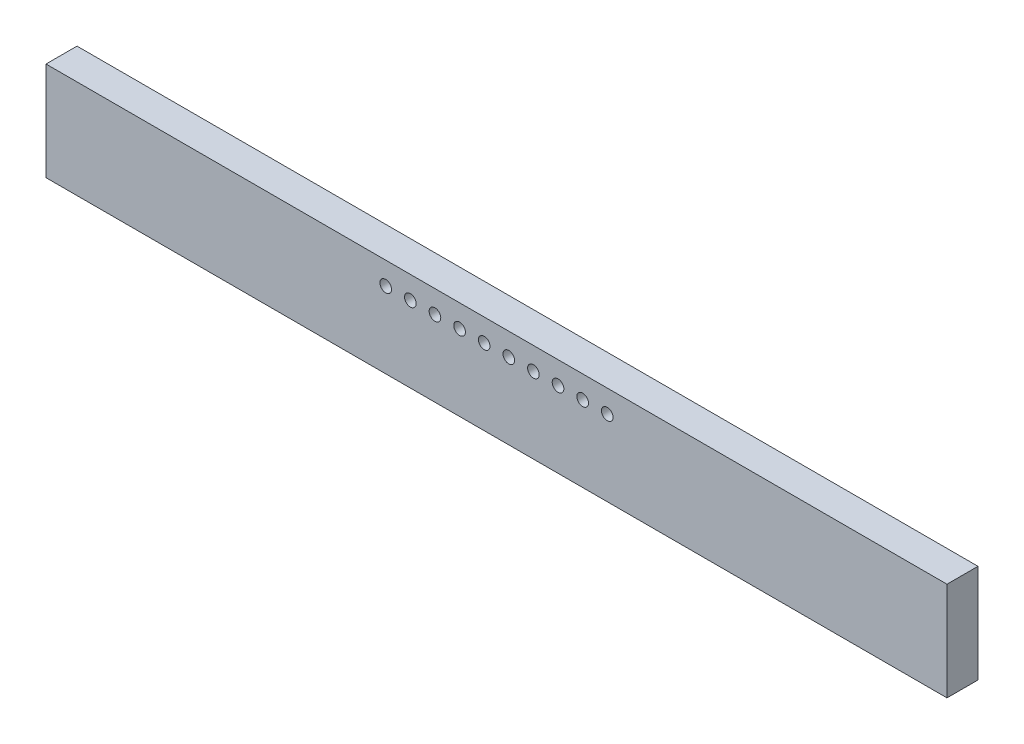
SolidWorks part; units mm, degrees
ref_plane "Front Plane" through (0, 0, 0) normal (0, 0, 1) x (1, 0, 0)
ref_plane "Top Plane" through (0, 0, 0) normal (0, 1, 0) x (1, 0, 0)
ref_plane "Right Plane" through (0, 0, 0) normal (1, 0, 0) x (0, 0, -1)
sketch "Sketch1" plane through (0, 0, 0) normal (0, 0, 1) x (1, 0, 0)
  line L1 (-23.241, -2.54) -> (23.241, -2.54)
  line L2 (-23.241, -2.54) -> (-23.241, 2.54)
  line L3 (-23.241, 2.54) -> (23.241, 2.54)
  line L4 (23.241, -2.54) -> (23.241, 2.54)
  line L5 (-23.241, -2.54) -> (23.241, 2.54) construction
  line L6 (-23.241, 2.54) -> (23.241, -2.54) construction
  point P0 (0, 0)
  dimension "D1" = 46.482
  dimension "D2" = 5.08
extrude "Boss-Extrude1" add sketch "Sketch1" along normal blind 1.6 contours L2 L1 L4 L3
sketch "Sketch2" plane through (0, 0, 1.6) normal (0, 0, 1) x (1, 0, 0)
  line L0 (-5.64, 1.305) -> (-5.79, 1.455) construction
  line L4 (-5.64, 1.455) -> (-5.79, 1.455)
  line L5 (-5.79, 1.455) -> (-5.79, 1.305)
  line L6 (-5.79, 1.305) -> (-5.64, 1.305)
  line L7 (-5.64, 1.305) -> (-5.64, 1.455)
  line L8 (-5.64, 1.455) -> (-5.79, 1.455)
  line L9 (-5.79, 1.455) -> (-5.79, 1.305)
  line L10 (-5.79, 1.305) -> (-5.64, 1.305)
  line L11 (-5.64, 1.305) -> (-5.64, 1.455)
  circle A0 centre (-5.715, 1.38) radius 0.3
  circle A1 centre (-4.445, 1.38) radius 0.3
  circle A2 centre (-3.175, 1.38) radius 0.3
  circle A3 centre (-1.905, 1.38) radius 0.3
  circle A4 centre (-0.635, 1.38) radius 0.3
  circle A5 centre (0.635, 1.38) radius 0.3
  circle A6 centre (1.905, 1.38) radius 0.3
  circle A7 centre (3.175, 1.38) radius 0.3
  circle A8 centre (4.445, 1.38) radius 0.3
  circle A9 centre (5.715, 1.38) radius 0.3
  dimension "D2" = 10
  dimension "D1" = 0
extrude "Cut-Extrude1" cut sketch "Sketch2" against normal through all
sketch "Sketch3" plane through (0, 0, 1.6) normal (0, 0, 1) x (1, 0, 0)
  line L0 (-23.241, 2.54) -> (-20.701, 0) construction
  line L1 (-20.701, 0) -> (-23.241, -2.54) construction
  line L2 (-23.241, -2.54) -> (-23.241, 2.54) construction
  line L5 (0, -0.88) -> (0, 0.88) construction
  line L6 (20.701, 0) -> (23.241, -2.54) construction
  line L7 (23.241, 2.54) -> (20.701, 0) construction
  line L8 (-20.701, 0) -> (20.701, 0) construction
  circle A0 centre (-5.715, 1.38) radius 0.3 construction
  point P3 (-19.901, 0)
  point P6 (-14.215, 0)
  point P7 (19.508, 0)
  point P8 (-8.529, 0)
  point P9 (-2.843, 0)
  point P16 (2.843, 0)
  point P17 (8.529, 0)
  point P18 (14.215, 0)
  point P19 (19.901, 0)
  dimension "D13" = 17.526
  dimension "D14" = 1.16
  dimension "D1" = 0.8
  dimension "D3" = 0.8
  dimension "D4" = 3.34
  dimension "D5" = 9.026
  dimension "D6" = 14.712
  dimension "D7" = 20.398
  dimension "D8" = 26.084
  dimension "D9" = 31.77
  dimension "D10" = 37.456
  dimension "D11" = 43.142
  dimension "D12" = 5.686
  dimension "D2" = 8
